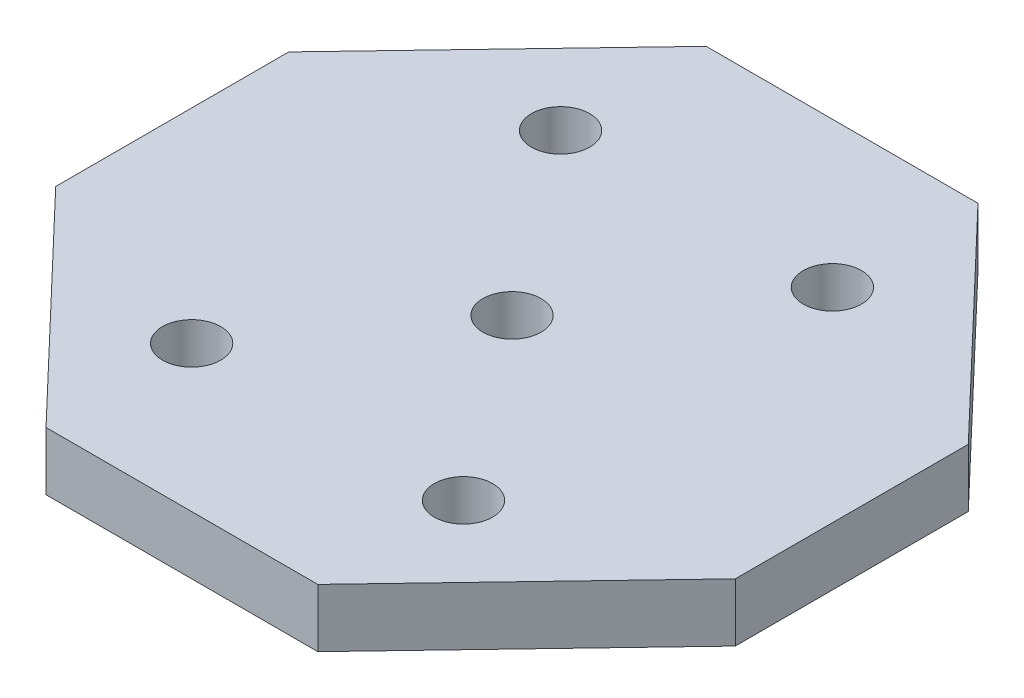
SolidWorks part; units mm, degrees
ref_plane "Front Plane" through (0, 0, 0) normal (0, 0, 1) x (1, 0, 0)
ref_plane "Top Plane" through (0, 0, 0) normal (0, 1, 0) x (1, 0, 0)
ref_plane "Right Plane" through (0, 0, 0) normal (1, 0, 0) x (0, 0, -1)
sketch "Sketch1" plane through (0, 0, 0) normal (0, 1, 0) x (1, 0, 0)
  line L0 (17.5, -6) -> (17.5, 6)
  line L1 (17.5, 6) -> (7, 17)
  line L2 (7, 17) -> (0, 17)
  line L3 (0, 17) -> (-7, 17)
  line L4 (-7, 17) -> (-17.5, 6)
  line L5 (-17.5, 6) -> (-17.5, -6)
  line L6 (-17.5, 0) -> (0, 0)
  line L7 (0, 0) -> (17.5, 0)
  line L8 (17.5, -6) -> (7, -17)
  line L9 (7, -17) -> (0, -17)
  line L10 (0, -17) -> (-7, -17)
  line L11 (-7, -17) -> (-17.5, -6)
  circle A0 centre (7, 9.5) radius 1.5
  circle A1 centre (-7, 9.5) radius 1.5
  circle A2 centre (7, -9.5) radius 1.5
  circle A3 centre (-7, -9.5) radius 1.5
  circle A4 centre (0, 0) radius 1.5
  dimension "D5" = 3
  dimension "D1" = 6
  dimension "D2" = 35
  dimension "D3" = 7
  dimension "D4" = 7
  dimension "D6" = 17
extrude "Boss-Extrude1" add sketch "Sketch1" along normal mid plane 3 contours A4 L7 L0 L1 L2 L3 L4 L5 L6 A1 A0 | A4 L6 L5 L11 L10 L9 L8 L0 L7 A2 A3
